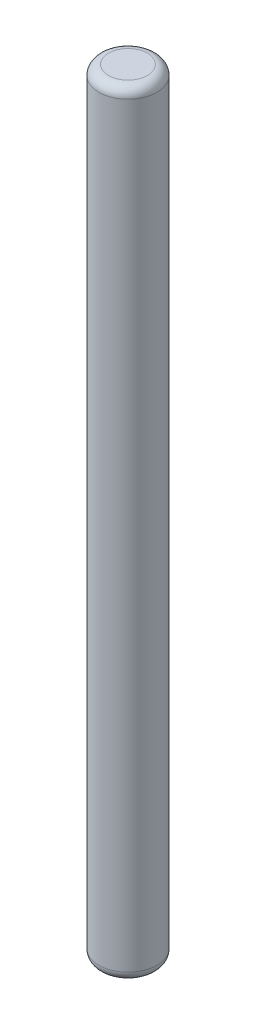
SolidWorks part; units mm, degrees
ref_plane "Front" through (0, 0, 0) normal (0, 0, 1) x (1, 0, 0)
ref_plane "Top" through (0, 0, 0) normal (0, 1, 0) x (1, 0, 0)
ref_plane "Right" through (0, 0, 0) normal (1, 0, 0) x (0, 0, -1)
sketch "Sketch2" plane through (0, 0, 0) normal (0, 1, 0) x (1, 0, 0)
  circle A0 centre (0, 0) radius 1.5
  dimension "D1" = 3
extrude "Boss-Extrude1" add sketch "Sketch2" along normal blind 40
fillet "Fillet1" radius 0.5 2 edges at (0, 40, 1.5) (0, 0, 1.5)
